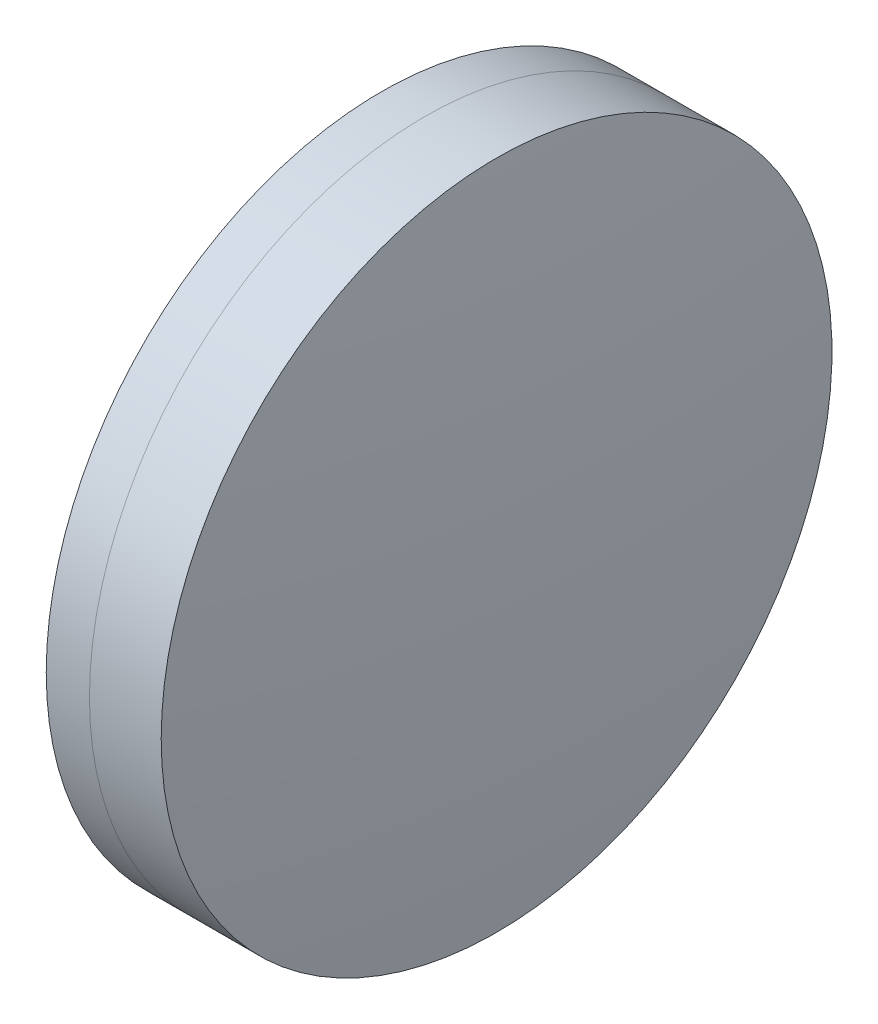
SolidWorks part; units mm, degrees
ref_plane "前视基准面" through (0, 0, 0) normal (0, 0, 1) x (1, 0, 0)
ref_plane "上视基准面" through (0, 0, 0) normal (0, 1, 0) x (1, 0, 0)
ref_plane "右视基准面" through (0, 0, 0) normal (1, 0, 0) x (0, 0, -1)
sketch "草图1" plane through (0, 0, 0) normal (0, 1, 0) x (1, 0, 0)
  line L0 (124.5233, 0) -> (646.9917, 0) construction
  line L1 (301.9579, -30) -> (305.8239, -30)
  line L2 (301.9579, 30) -> (305.8239, 30)
  arc A0 (305.8239, -30) -> (305.8239, 30) centre (216.1226, 0) ccw
  arc A1 (301.9579, 30) -> (301.9579, -30) centre (425.5006, 0) ccw
  point P10 (298.3676, 0)
  point P11 (310.7076, 0)
  dimension "D3" = 127.133
  dimension "D4" = 94.585
  dimension "D1" = 30
  dimension "D2" = 30
  dimension "D5" = 12.34
revolve "旋转1" add sketch "草图1" angle 360 about L0
sketch "草图2" plane through (0, 0, 0) normal (0, 1, 0) x (1, 0, 0)
  line L0 (-0.5519, 0) -> (622.6607, 0) construction
  line L2 (305.8239, 30) -> (312.2419, 30)
  line L3 (305.8239, -30) -> (312.2419, -30)
  arc A0 (312.2419, -30) -> (312.2419, 30) centre (31.0376, 0) ccw
  arc A1 (305.8239, -30) -> (305.8239, 30) centre (216.1226, 0) ccw construction
  arc A2 (305.8239, -30) -> (305.8239, 30) centre (216.1226, 0) ccw
  point P4 (310.7076, 0)
  point P8 (313.8376, 0)
  dimension "D1" = 282.8
  dimension "D2" = 3.13
revolve "旋转3" add sketch "草图2" angle 360 about L0
